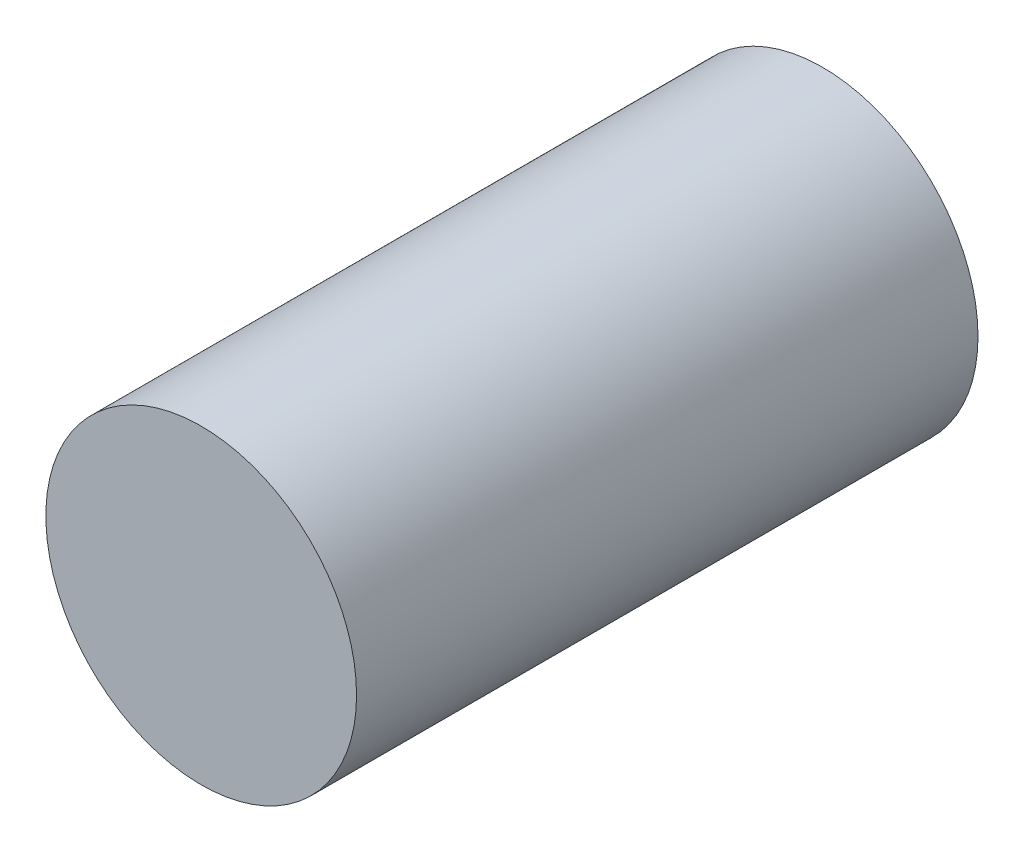
SolidWorks part; units mm, degrees
ref_plane "前视基准面" through (0, 0, 0) normal (0, 0, 1) x (1, 0, 0)
ref_plane "上视基准面" through (0, 0, 0) normal (0, 1, 0) x (1, 0, 0)
ref_plane "右视基准面" through (0, 0, 0) normal (1, 0, 0) x (0, 0, -1)
sketch "草图1" plane through (0, 0, 0) normal (0, 0, 1) x (1, 0, 0)
  circle A0 centre (0, 0) radius 3
extrude "凸台-拉伸1" add sketch "草图1" along normal blind 12
